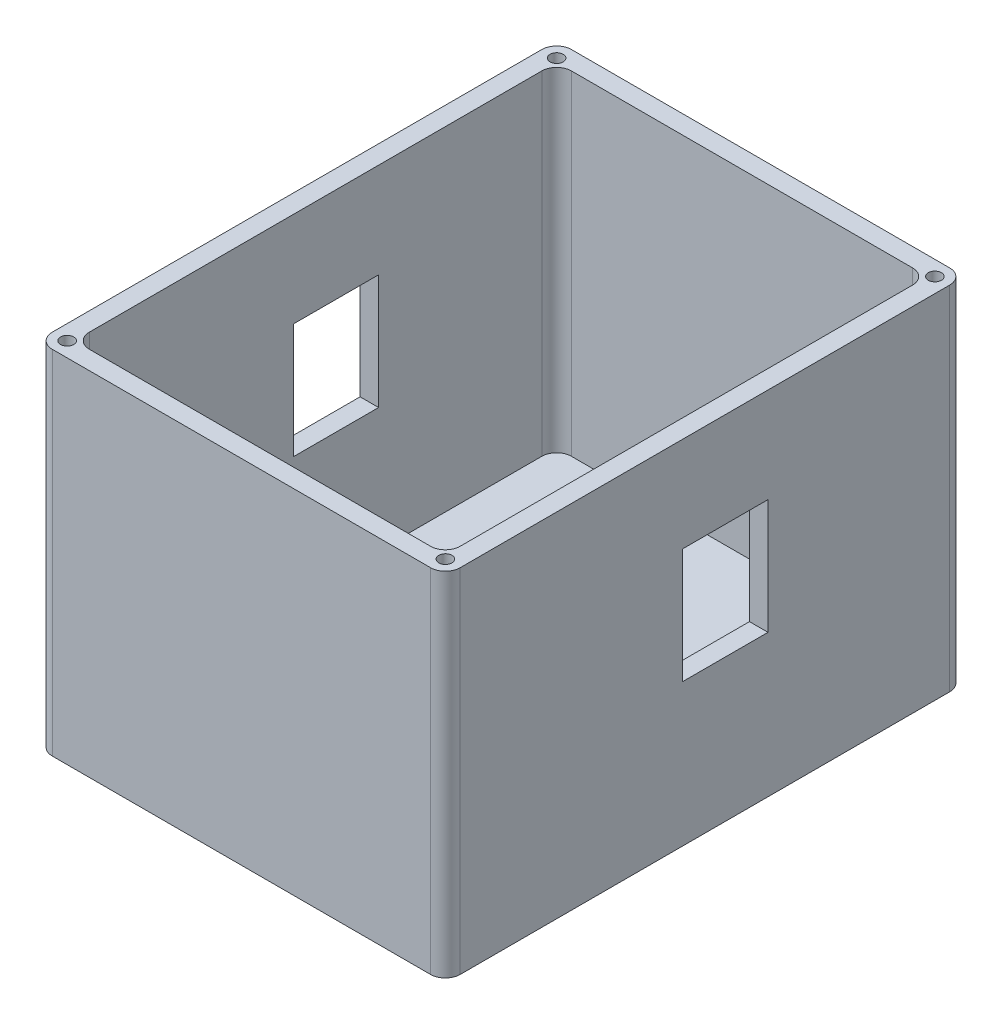
SolidWorks part; units mm, degrees
ref_plane "Front Plane" through (0, 0, 0) normal (0, 0, 1) x (1, 0, 0)
ref_plane "Top Plane" through (0, 0, 0) normal (0, 1, 0) x (1, 0, 0)
ref_plane "Right Plane" through (0, 0, 0) normal (1, 0, 0) x (0, 0, -1)
sketch "Sketch1" plane through (0, 0, 0) normal (0, 1, 0) x (1, 0, 0)
  line L1 (0, 0) -> (63.5, 0)
  line L2 (0, 0) -> (0, -82.55)
  line L3 (0, -82.55) -> (63.5, -82.55)
  line L4 (63.5, 0) -> (63.5, -82.55)
  dimension "D1" = 63.5
  dimension "D2" = 82.55
extrude "Boss-Extrude1" add sketch "Sketch1" along normal blind 57.15
shell "Shell1" thickness 3.175
sketch "Sketch2" plane through (0, 0, 0) normal (0, 1, 0) x (1, 0, 0)
  line L0 (0, 0) -> (0, -82.55) construction
  line L2 (63.5, -82.55) -> (63.5, 0) construction
  line L3 (63.5, 0) -> (0, 0) construction
  circle A0 centre (12.827, -68.58) radius 0.9525
  circle A1 centre (40.132, -68.58) radius 0.9525
  circle A2 centre (56.007, -17.78) radius 0.9525
  dimension "D1" = 12.827
  dimension "D3" = 1.905
  dimension "D2" = 50.8
  dimension "D4" = 27.305
  dimension "D5" = 7.493
  dimension "D6" = 17.78
sketch "Sketch3" plane through (0, 0, 0) normal (0, 1, 0) x (1, 0, 0)
  circle A0 centre (12.827, -68.58) radius 3.175
  circle A1 centre (40.132, -68.58) radius 3.175
  circle A2 centre (56.007, -17.78) radius 3.175
  dimension "D1" = 6.35
extrude "Boss-Extrude2" add sketch "Sketch3" along normal blind 3.175
extrude "Cut-Extrude1" cut sketch "Sketch2" against normal blind 0.0127 and the other way blind 6.35
fillet "Fillet1" radius 2.54 8 edges at (-3.175, 26.9875, 85.725) (-3.175, 26.9875, -3.175) (0, 28.575, 82.55) (0, 28.575, 0) (66.675, 26.9875, -3.175) (66.675, 26.9875, 85.725) (63.5, 28.575, 82.55) (63.5, 28.575, 0)
sketch "Sketch4" plane through (0, 0, 0) normal (0, 0, 1) x (1, 0, 0)
  line L0 (59.182, 3.175) -> (52.832, 3.175) construction
  line L1 (36.703, 15.748) -> (48.895, 15.748)
  line L2 (36.703, 15.748) -> (36.703, 4.826)
  line L3 (36.703, 4.826) -> (48.895, 4.826)
  line L4 (48.895, 15.748) -> (48.895, 4.826)
  line L5 (63.5, 57.15) -> (63.5, 0) construction
  dimension "D1" = 10.922
  dimension "D2" = 12.192
  dimension "D3" = 1.651
  dimension "D4" = 14.605
extrude "Cut-Extrude2" cut sketch "Sketch4" against normal through all
sketch "Sketch5" plane through (66.675, 0, 0) normal (1, 0, 0) x (0, 0, -1)
  line L1 (-45.085, 40.894) -> (-30.48, 40.894)
  line L2 (-45.085, 40.894) -> (-45.085, 21.209)
  line L3 (-45.085, 21.209) -> (-30.48, 21.209)
  line L4 (-30.48, 40.894) -> (-30.48, 21.209)
  line L5 (-14.605, 3.175) -> (-20.955, 3.175) construction
  line L6 (0, 0) -> (0, 57.15) construction
  dimension "D1" = 19.685
  dimension "D2" = 14.605
  dimension "D3" = 18.034
  dimension "D4" = 30.48
extrude "Cut-Extrude3" cut sketch "Sketch5" against normal through all
hole_wizard "#4-40 Tapped Hole1" positions "Sketch6" profile "Sketch7" tap size "#4-40" standard "ANSI Inch"
sketch "Sketch6" plane through (0, 57.15, 0) normal (0, 1, 0) x (1, 0, 0)
  arc A0 (-0.635, 3.175) -> (-3.175, 0.635) centre (-0.635, 0.635) ccw construction
  arc A1 (66.675, 0.635) -> (64.135, 3.175) centre (64.135, 0.635) ccw construction
  arc A2 (64.135, -85.725) -> (66.675, -83.185) centre (64.135, -83.185) ccw construction
  arc A3 (-3.175, -83.185) -> (-0.635, -85.725) centre (-0.635, -83.185) ccw construction
  point P0 (64.135, -83.185)
  point P2 (-0.635, -83.185)
  point P4 (-0.635, 0.635)
  point P6 (64.135, 0.635)
  point P9 (0, 0)
  point P10 (0, 0)
  point P14 (0, 0)
  point P18 (0, 0)
  point P22 (0, 0)
sketch "Sketch7" plane through (64.135, 57.15, 83.185) normal (1, 0, 0) x (0, 0, 1)
  line L0 (0, 0) -> (0, 7.0292)
  line L1 (0, 7.0292) -> (1.1303, 6.35)
  line L2 (1.1303, 6.35) -> (1.1303, 0)
  line L5 (1.1303, 0) -> (0, 0)
  line L10 (0, 7.0292) -> (-1.1303, 6.35) construction
  line L11 (0, -6.35) -> (0, 107.95) construction
  dimension "Tap Drill Dia." = 2.2606
  dimension "Tap Drill Depth" = 6.35
  dimension "Drill Angle" = 118
cosmetic thread "Hole Thread1" parameters "D1"=3.048, "D2"=2.8448
cosmetic thread "Hole Thread2" parameters "D1"=3.048, "D2"=2.8448
cosmetic thread "Hole Thread3" parameters "D1"=3.048, "D2"=2.8448
cosmetic thread "Hole Thread4" parameters "D1"=3.048, "D2"=2.8448
